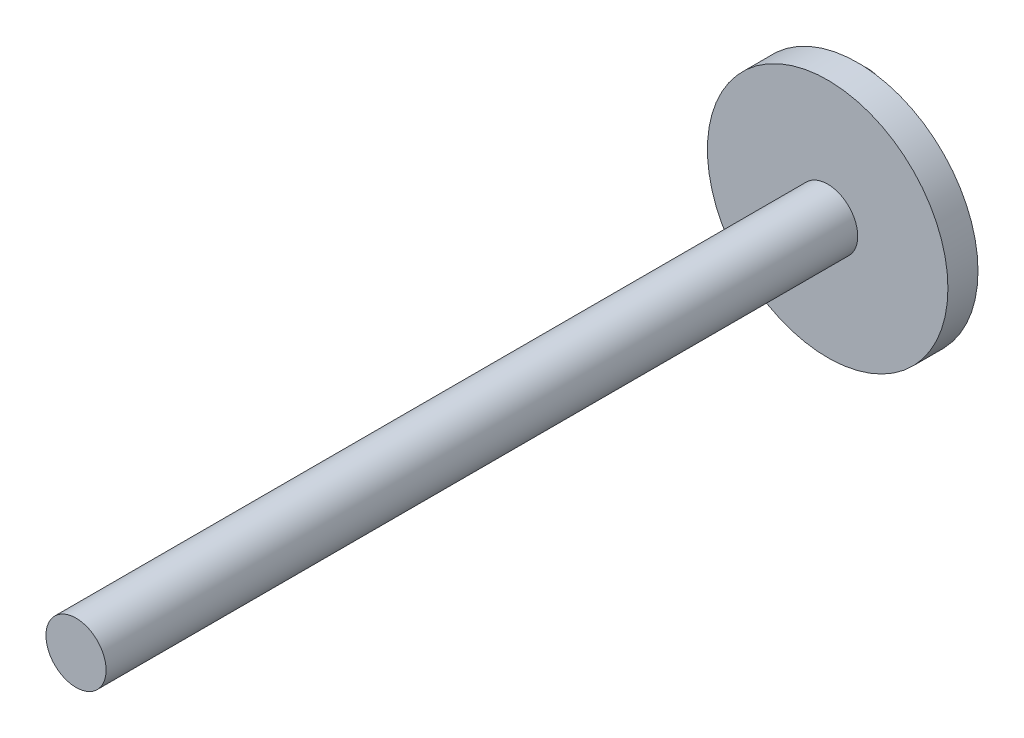
SolidWorks part; units mm, degrees
ref_plane "Front Plane" through (0, 0, 0) normal (0, 0, 1) x (1, 0, 0)
ref_plane "Top Plane" through (0, 0, 0) normal (0, 1, 0) x (1, 0, 0)
ref_plane "Right Plane" through (0, 0, 0) normal (1, 0, 0) x (0, 0, -1)
sketch "Sketch1" plane through (0, 0, 0) normal (0, 0, 1) x (1, 0, 0)
  circle A0 centre (0, 0) radius 40
  dimension "D1" = 80
extrude "Boss-Extrude1" add sketch "Sketch1" along normal blind 10
sketch "Sketch2" plane through (0, 0, 10) normal (0, 0, 1) x (1, 0, 0)
  circle A0 centre (0, 0) radius 10
extrude "Boss-Extrude2" add sketch "Sketch2" along normal blind 250
sketch "Sketch3" plane through (0, 0, 0) normal (0, 0, -1) x (-1, 0, 0)
  circle A0 centre (26.9986, 0) radius 10
extrude "Boss-Extrude3" add sketch "Sketch3" along normal blind 30
